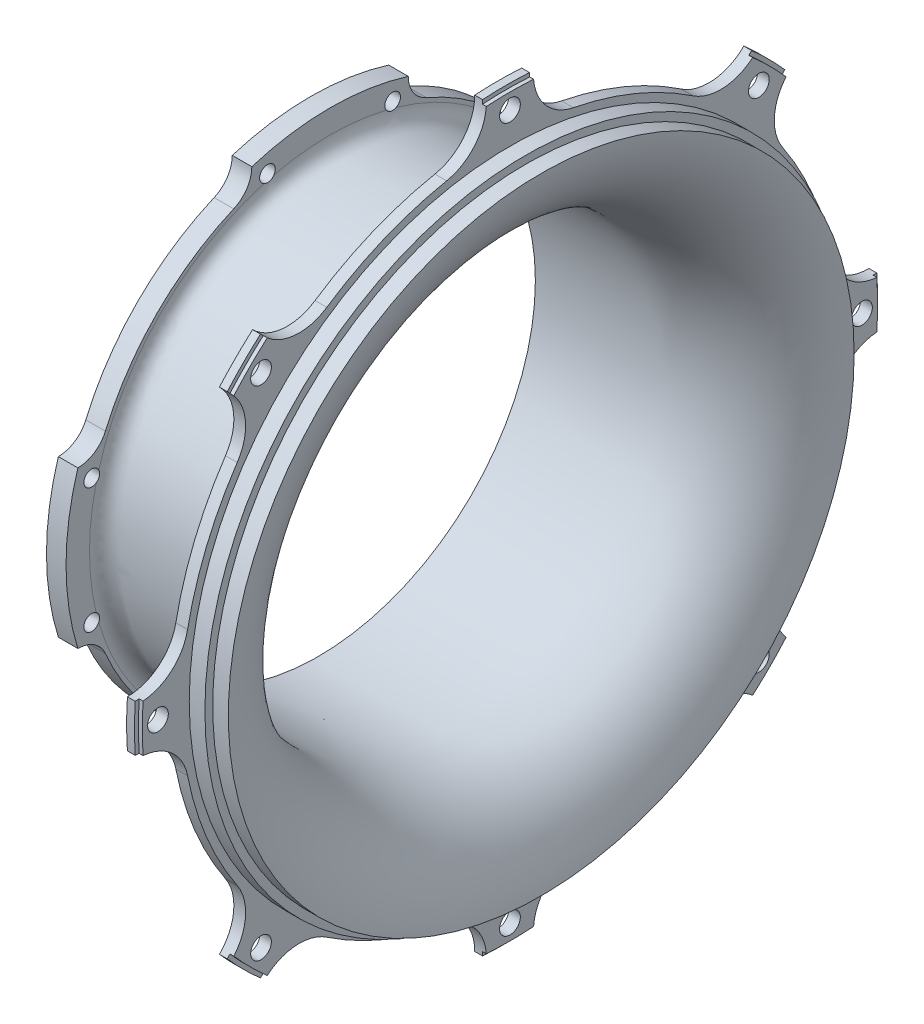
SolidWorks part; units mm, degrees
material "7075-O (SS)"
ref_plane "Front Plane" through (0, 0, 0) normal (0, 0, 1) x (1, 0, 0)
ref_plane "Top Plane" through (0, 0, 0) normal (0, 1, 0) x (1, 0, 0)
ref_plane "Right Plane" through (0, 0, 0) normal (1, 0, 0) x (0, 0, -1)
sketch "Sketch1" plane through (0, 0, 0) normal (0, 0, 1) x (1, 0, 0)
  line L0 (-30.116, 55.5) -> (0, 55.5) construction
  line L1 (26.884, 80) -> (22.884, 80)
  line L2 (22.884, 80) -> (22.884, 82)
  line L3 (22.884, 82) -> (18.884, 82)
  line L4 (18.884, 82) -> (18.884, 84)
  line L5 (18.884, 84) -> (15.884, 84)
  line L6 (21.0607, 0) -> (-16.4592, 0) construction
  line L7 (15.884, 84) -> (15.884, 81)
  line L8 (15.884, 81) -> (22.9047, 78.3951)
  line L9 (-27.116, 61.5) -> (-27.116, 62.5)
  line L10 (-32.116, 62.5) -> (-32.116, 58.5)
  line L11 (-27.116, 62.5) -> (-32.116, 62.5)
  line L12 (-32.116, 58.5) -> (-30.116, 58.5)
  line L13 (-30.116, 58.5) -> (-30.116, 55.5)
  line L14 (0, 57.5) -> (-23.116, 57.5) construction
  arc A0 (0, 55.5) -> (26.884, 80) centre (0, 82.5) ccw construction
  arc A1 (0, 57.5) -> (24.1402, 76) centre (0, 82.5) ccw construction
  arc A2 (22.9047, 78.3951) -> (24.1402, 76) centre (22.209, 76.52) cw
  arc A3 (-23.116, 57.5) -> (-27.116, 61.5) centre (-23.116, 61.5) cw construction
  spline S0 degree 3 poles (26.884, 80) (25.9095, 69.5208) (19.5655, 61.1235) (9.7515, 57.3225) (8.7236, 56.9244) (6.6191, 56.254) (3.3068, 55.5) (1.1023, 55.5) (0, 55.5) (-0.8366, 55.5) (-2.5097, 55.5) (-5.0193, 55.5) (-6.6924, 55.5) (-7.529, 55.5) (-15.058, 55.5) (-22.587, 55.5) (-30.116, 55.5) knots 0 0 0 0 0.41517 0.41517 0.41517 0.463474 0.511777 0.560081 0.560081 0.560081 0.596741 0.633401 0.670061 0.670061 0.670061 1 1 1 1 weights 1 0.900188 0.900188 1 1 1 1 1 1 1 1 1 1 1 1 1 1
  spline S1 degree 3 poles (24.1402, 76) (21.9252, 67.7737) (16.0967, 61.5603) (8.0287, 58.8243) (7.1725, 58.5339) (5.4285, 58.0461) (2.7124, 57.5) (0.9041, 57.5) (0, 57.5) (-0.6421, 57.5) (-1.9263, 57.5) (-3.8527, 57.5) (-5.1369, 57.5) (-5.779, 57.5) (-11.0378, 57.5) (-16.2965, 57.5) (-21.5553, 57.5) (-21.7287, 57.5) (-22.0755, 57.5) (-22.5957, 57.5) (-22.9426, 57.5) (-23.116, 57.5) (-23.2894, 57.5) (-23.6362, 57.5) (-24.1575, 57.6262) (-24.4865, 57.7381) (-24.6467, 57.8045) (-26.1887, 58.4432) (-27.116, 59.831) (-27.116, 61.5) knots 0 0 0 0 0.387277 0.387277 0.387277 0.431884 0.47649 0.521096 0.521096 0.521096 0.552775 0.584453 0.616132 0.616132 0.616132 0.875576 0.875576 0.875576 0.884131 0.892687 0.901242 0.901242 0.901242 0.909798 0.918353 0.926908 0.926908 0.926908 1 1 1 1 weights 1 0.921425 0.921425 1 1 1 1 1 1 1 1 1 1 1 1 1 1 1 1 1 1 1 1 1 1 1 1 0.887646 0.887646 1
  dimension "D1" = 27
  dimension "D9" = 2
  dimension "D13" = 2
  dimension "D16" = 4
  dimension "D2" = 111
  dimension "D3" = 160
  dimension "D4" = 4
  dimension "D5" = 4
  dimension "D6" = 59
  dimension "D7" = 164
  dimension "D8" = 168
  dimension "D10" = 152
  dimension "D11" = 3
  dimension "D12" = 162
  dimension "D14" = 5
  dimension "D15" = 125
  dimension "D17" = 2
  dimension "D18" = 117
revolve "Revolve1" add sketch "Sketch1" angle 360 about L6
sketch "Sketch2" plane through (15.884, 0, 0) normal (-1, 0, 0) x (0, 0, 1)
  line L0 (0, 96.7815) -> (0, 74.185) construction
  arc A0 (6, 94.8103) -> (-6, 94.8103) centre (0, 0) ccw
  circle A1 centre (0, 0) radius 84 construction
  arc A2 (16.1892, 82.4252) -> (-16.1892, 82.4252) centre (0, 0) ccw
  arc A3 (-6, 94.8103) -> (-16.1892, 82.4252) centre (-18.6218, 94.8103) cw
  arc A4 (6, 94.8103) -> (16.1892, 82.4252) centre (18.6218, 94.8103) ccw
  dimension "D1" = 190
  dimension "D2" = 12
extrude "Boss-Extrude1" add sketch "Sketch2" against normal up to surface (3 mm away) up to face at (18.884, 0, -84)
hole_wizard "M5 Clearance Hole1" positions "Sketch5" profile "Sketch6" hole size "M5" standard "DIN" end condition up to next
sketch "Sketch5" plane through (15.884, 0, 0) normal (-1, 0, 0) x (0, 0, 1)
  point P0 (0, 90)
  dimension "D1" = 90
sketch "Sketch6" plane through (15.884, 90, 0) normal (0, 1, 0) x (0, 0, 1)
  line L0 (0, 0) -> (0, 3.001)
  line L1 (0, 3.001) -> (2.65, 3.001)
  line L2 (2.65, 3.001) -> (2.65, 0)
  line L5 (2.65, 0) -> (0, 0)
  line L11 (0, -6.35) -> (0, 107.95) construction
  dimension "Thru Hole Dia." = 5.3
  dimension "Thru Hole Depth" = 3.001
pattern_circular "CirPattern2" count 8 over 360 about axis through (0, 0, 0) along (1, 0, 0) of "Boss-Extrude1", "M5 Clearance Hole1"
sketch "Sketch3" plane through (0, 0, 0) normal (0, 0, 1) x (1, 0, 0)
  line L0 (-27.6698, 0) -> (41.6737, 0) construction
  line L1 (18.884, 95) -> (17.884, 95)
  line L2 (18.884, 95) -> (18.884, 94)
  line L3 (18.884, 94) -> (17.884, 94)
  line L4 (17.884, 95) -> (17.884, 94)
  dimension "D1" = 1
  dimension "D2" = 1
revolve "Cut-Revolve1" cut sketch "Sketch3" angle 360 about L0
sketch "Sketch8" plane through (-32.116, 0, 0) normal (-1, 0, 0) x (0, 0, 1)
  line L0 (0, 50.4654) -> (0, 45.6756) construction
  arc A0 (20, 64.469) -> (-20, 64.469) centre (0, 0) ccw
  circle A1 centre (0, 0) radius 62.5 construction
  arc A2 (24.6331, 57.4409) -> (-24.6331, 57.4409) centre (0, 0) ccw
  arc A3 (-20, 64.469) -> (-24.6331, 57.4409) centre (-27.6471, 64.469) cw
  arc A4 (20, 64.469) -> (24.6331, 57.4409) centre (27.6471, 64.469) ccw
  dimension "D1" = 135
  dimension "D2" = 40
extrude "Boss-Extrude2" add sketch "Sketch8" against normal up to surface (5 mm away) up to face at (-27.116, 0, -62.5)
hole_wizard "M4 Tapped Hole1" positions "Sketch10" profile "Sketch9" tap size "M4" standard "DIN"
sketch "Sketch10" plane through (-32.116, 0, 0) normal (-1, 0, 0) x (0, 0, 1)
  line L0 (0, 15.5082) -> (0, -6.4626) construction
  circle A0 centre (0, 0) radius 63 construction
  point P0 (-16, 60.9344)
  point P10 (16, 60.9344)
  dimension "D1" = 126
  dimension "D2" = 32
sketch "Sketch9" plane through (-32.116, 60.9344, -16) normal (0, 1, 0) x (0, 0, 1)
  line L0 (0, 0) -> (0, 11.2414)
  line L1 (0, 11.2414) -> (1.65, 10.25)
  line L2 (1.65, 10.25) -> (1.65, 8)
  line L3 (1.65, 8) -> (2, 8)
  line L4 (2, 8) -> (2, 0)
  line L5 (2, 0) -> (0, 0)
  line L10 (0, 11.2414) -> (-1.65, 10.25) construction
  line L11 (0, -6.35) -> (0, 107.95) construction
  dimension "Tap Drill Dia." = 3.3
  dimension "Tap Drill Depth" = 10.25
  dimension "Thread Major Dia." = 4
  dimension "Thread Depth" = 8
  dimension "Drill Angle" = 118
pattern_circular "CirPattern3" count 4 over 360 about axis through (0, 0, 0) along (1, 0, 0) of "M4 Tapped Hole1", "Boss-Extrude2"
